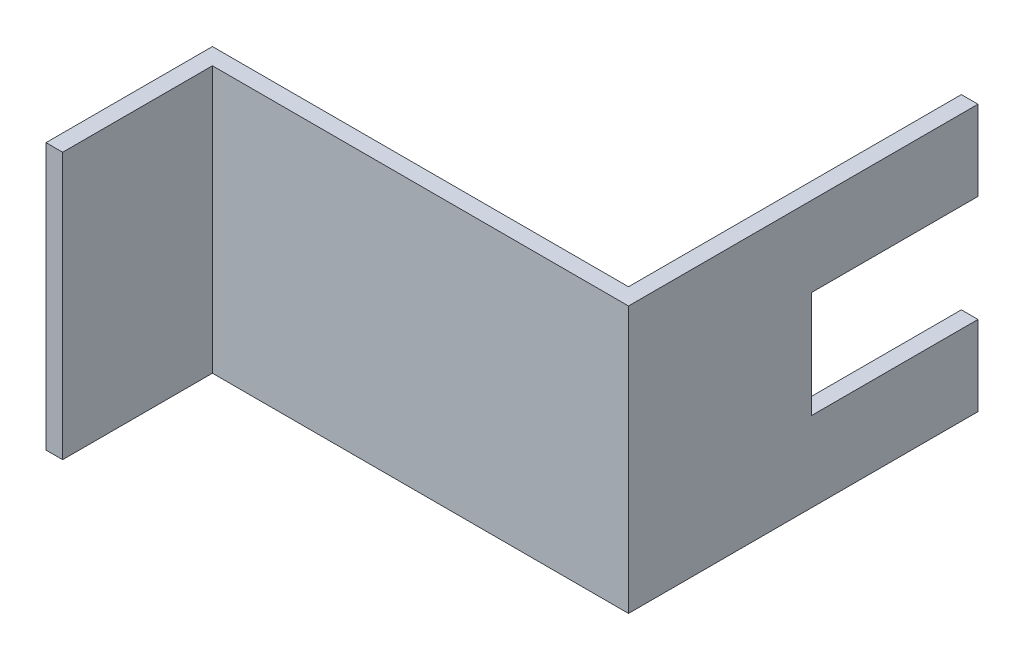
SolidWorks part; units mm, degrees
ref_plane "Front Plane" through (0, 0, 0) normal (0, 0, 1) x (1, 0, 0)
ref_plane "Top Plane" through (0, 0, 0) normal (0, 1, 0) x (1, 0, 0)
ref_plane "Right Plane" through (0, 0, 0) normal (1, 0, 0) x (0, 0, -1)
sketch "Sketch1" plane through (0, 0, 0) normal (0, 1, 0) x (1, 0, 0)
  line L0 (24.8889, 23.6841) -> (24.8889, -8.0659)
  line L1 (24.8889, -8.0659) -> (-14.7986, -8.0659)
  line L2 (-14.7986, -8.0659) -> (-14.7986, -23.9409)
  line L3 (-14.7986, -23.9409) -> (-13.2111, -23.9409)
  line L4 (-13.2111, -23.9409) -> (-13.2111, -9.6534)
  line L5 (-13.2111, -9.6534) -> (26.4764, -9.6534)
  line L6 (26.4764, -9.6534) -> (26.4764, 23.6841)
  line L7 (26.4764, 23.6841) -> (27.6947, 23.6841)
  line L8 (-14.7986, -23.9409) -> (-14.7986, -8.0659)
  line L10 (-14.7986, -23.9409) -> (-13.2111, -23.9409)
  line L11 (-14.7986, -23.9409) -> (-14.7986, -8.0659)
  line L12 (-14.7986, -8.0659) -> (-13.2111, -8.0659)
  line L13 (-13.2111, -23.9409) -> (-13.2111, -8.0659)
  line L14 (26.4764, -9.6534) -> (24.8889, -9.6534)
  line L15 (26.4764, -9.6534) -> (26.4764, 23.6841)
  line L16 (26.4764, 23.6841) -> (24.8889, 23.6841)
  line L17 (24.8889, -9.6534) -> (24.8889, 23.6841)
  line L18 (24.8889, -8.0659) -> (-13.2111, -8.0659)
  line L19 (24.8889, -8.0659) -> (24.8889, -9.6534)
  line L20 (24.8889, -9.6534) -> (-13.2111, -9.6534)
  line L21 (-13.2111, -8.0659) -> (-13.2111, -9.6534)
  dimension "D1" = 1.5875
  dimension "D2" = 1.5875
  dimension "D3" = 1.5875
  dimension "D4" = 31.75
  dimension "D5" = 41.275
  dimension "D7" = 47.625
extrude "Boss-Extrude1" add sketch "Sketch1" along normal blind 25.4 contours L4 L13 L1 L2 L3 | L5 L17 L1 L13 | L17 L5 L6 L7 L16 L0
sketch "Sketch2" plane through (26.4764, 0, 0) normal (1, 0, 0) x (0, 0, -1)
  line L1 (23.6841, 17.78) -> (7.8091, 17.78)
  line L2 (23.6841, 17.78) -> (23.6841, 7.62)
  line L3 (23.6841, 7.62) -> (7.8091, 7.62)
  line L4 (7.8091, 17.78) -> (7.8091, 7.62)
  line L5 (-9.6534, 25.4) -> (23.6841, 25.4) construction
  line L7 (23.6841, 25.4) -> (23.6841, 0) construction
  dimension "D1" = 10.16
  dimension "D2" = 7.62
  dimension "D3" = 15.875
  dimension "D4" = 0
extrude "Cut-Extrude1" cut sketch "Sketch2" against normal blind 25.4
